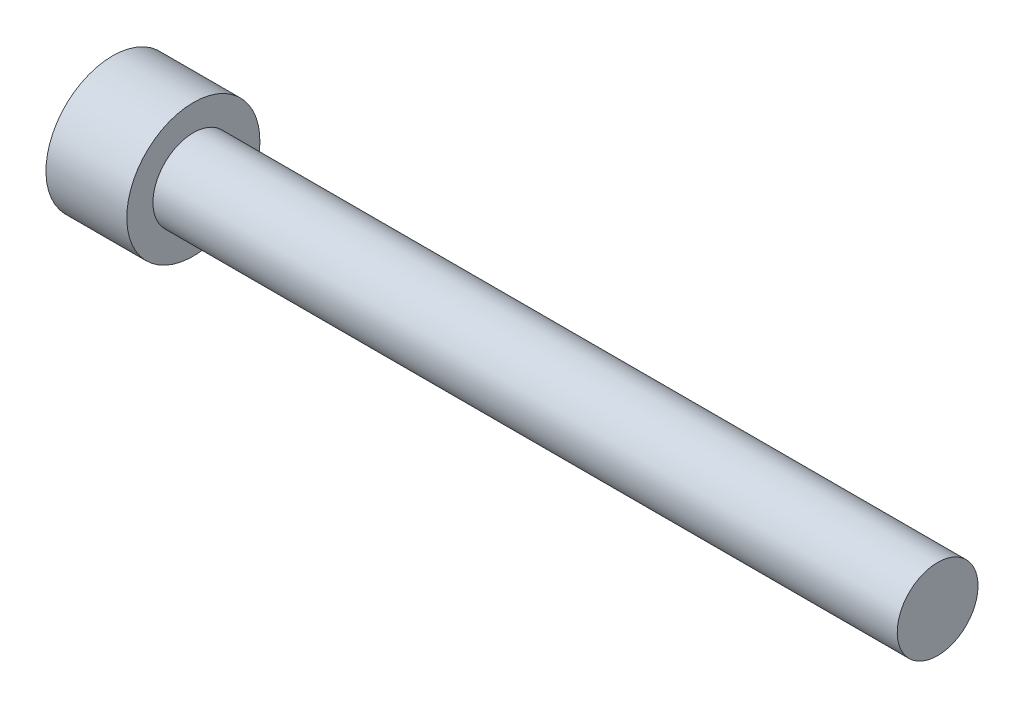
SolidWorks part; units mm, degrees
material "Plain Carbon Steel"
ref_plane "Front Plane" through (0, 0, 0) normal (0, 0, 1) x (1, 0, 0)
ref_plane "Top Plane" through (0, 0, 0) normal (0, 1, 0) x (1, 0, 0)
ref_plane "Right Plane" through (0, 0, 0) normal (1, 0, 0) x (0, 0, -1)
sketch "Sketch1" plane through (0, 0, 0) normal (0, 0, 1) x (1, 0, 0)
  line L0 (0, 2.413) -> (44.45, 2.413)
  line L1 (44.45, 2.413) -> (44.45, 0)
  line L2 (44.45, 0) -> (-4.826, 0)
  line L3 (-4.826, 0) -> (-4.826, 3.9751)
  line L4 (-4.826, 3.9751) -> (0, 3.9751)
  line L5 (0, 3.9751) -> (0, 2.413)
  dimension "D1" = 44.45
  dimension "D2" = 4.826
  dimension "D3" = 2.413
  dimension "D4" = 3.9751
revolve "Revolve1" add sketch "Sketch1" angle 360 about L2
